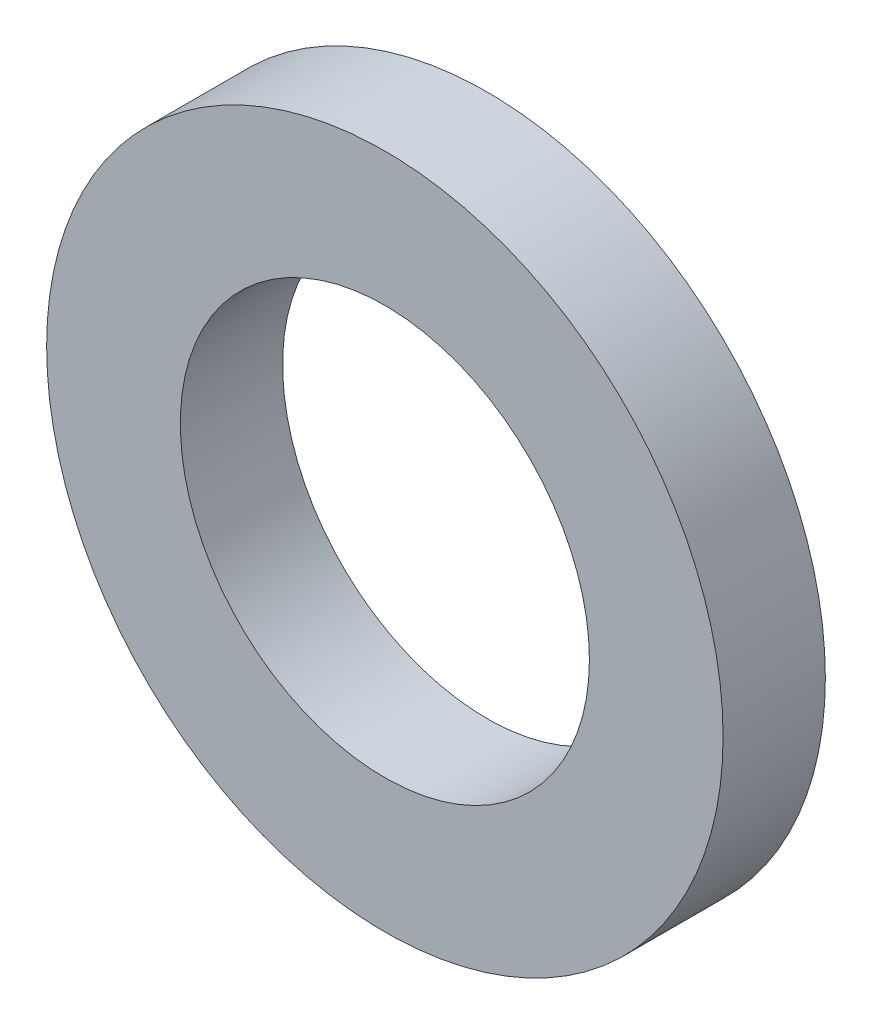
SolidWorks part; units mm, degrees
ref_plane "Front Plane" through (0, 0, 0) normal (0, 0, 1) x (1, 0, 0)
ref_plane "Top Plane" through (0, 0, 0) normal (0, 1, 0) x (1, 0, 0)
ref_plane "Right Plane" through (0, 0, 0) normal (1, 0, 0) x (0, 0, -1)
sketch "Sketch1" plane through (0, 0, 0) normal (0, 0, 1) x (1, 0, 0)
  circle A0 centre (0, 0) radius 10.5
  circle A1 centre (0, 0) radius 7.5
  point P4 (0, 0)
  dimension "D1" = 21
  dimension "D2" = 15
extrude "Boss-Extrude1" add sketch "Sketch1" along normal blind 3.175 contours A1 | A0
sketch "Sketch2" plane through (0, 0, 0) normal (0, 0, 1) x (1, 0, 0)
  circle A0 centre (0, 0) radius 7.5
  circle A1 centre (0, 0) radius 6.35
  dimension "D1" = 12.7
extrude "Boss-Extrude2" add sketch "Sketch2" along normal blind 3.175
